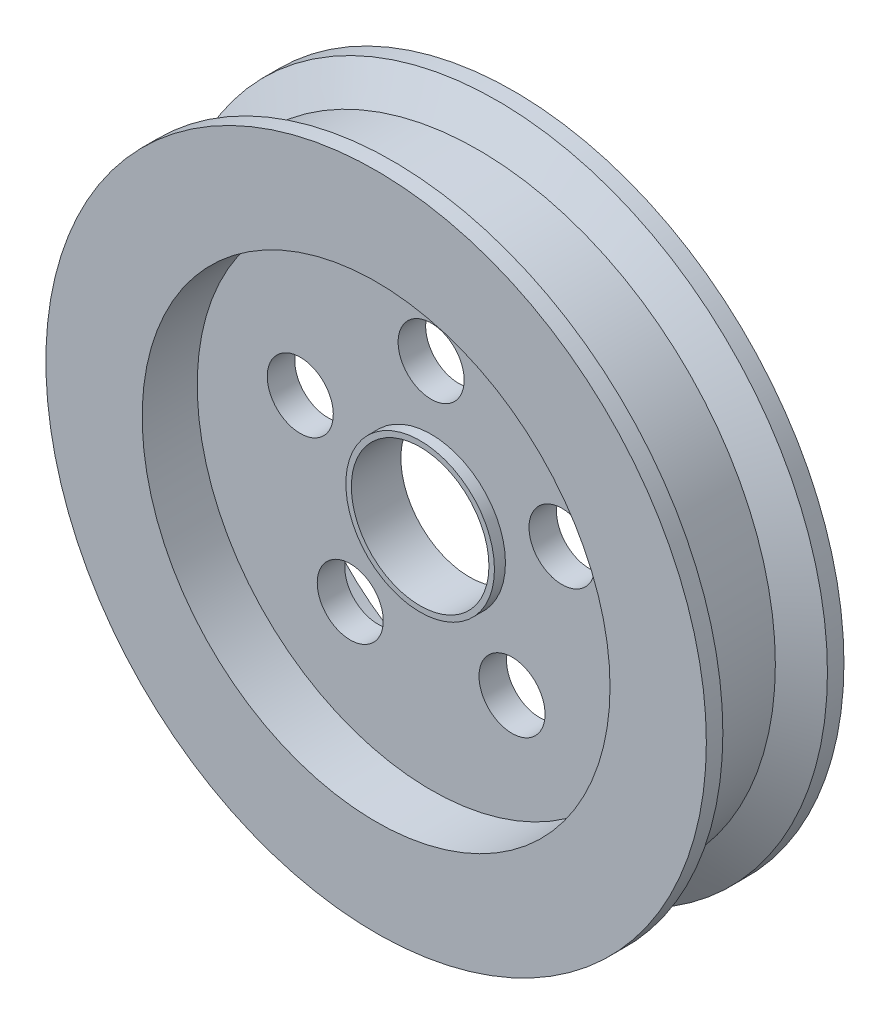
SolidWorks part; units mm, degrees
ref_plane "Front Plane" through (0, 0, 0) normal (0, 0, 1) x (1, 0, 0)
ref_plane "Top Plane" through (0, 0, 0) normal (0, 1, 0) x (1, 0, 0)
ref_plane "Right Plane" through (0, 0, 0) normal (1, 0, 0) x (0, 0, -1)
sketch "Sketch1" plane through (0, 0, 0) normal (0, 0, 1) x (1, 0, 0)
  circle A0 centre (0, 0) radius 60
  circle A1 centre (0, 0) radius 12.5
  dimension "D1" = 120
  dimension "D2" = 25
extrude "Boss-Extrude1" add sketch "Sketch1" along normal mid plane 25
sketch "Sketch2" plane through (0, 0, 12.5) normal (0, 0, 1) x (1, 0, 0)
  circle A0 centre (0, 0) radius 42.5
  dimension "D1" = 85
extrude "Cut-Extrude1" cut sketch "Sketch2" against normal blind 10
mirror "Mirror1" about plane through (0, 0, 0) normal (0, 0, 1) of "Cut-Extrude1"
sketch "Sketch3" plane through (0, 0, 2.5) normal (0, 0, 1) x (1, 0, 0)
  circle A0 centre (0, 25) radius 6
  dimension "D1" = 12
  dimension "D2" = 25
extrude "Cut-Extrude2" cut sketch "Sketch3" against normal through all
pattern_circular "CirPattern1" count 5 over 360 about axis through (0, 0, 0) along (0, 0, 1) of "Cut-Extrude2"
sketch "Sketch4" plane through (0, 0, 0) normal (0, 1, 0) x (1, 0, 0)
  line L0 (0, 0) -> (0, 42.4547) construction
  line L1 (60, 9.5) -> (54, 6.0359)
  line L2 (60, -12.5) -> (60, 12.5) construction
  line L6 (60, -9.5) -> (54, -6.0359)
  line L7 (54, -6.0359) -> (54, 6.0359)
  line L8 (60, -9.5) -> (60, 9.5)
  point P9 (60, 0)
  dimension "D1" = 3
  dimension "D2" = 3
  dimension "D3" = 6
  dimension "D4" = 60
  dimension "D5" = 60
revolve "Cut-Revolve1" cut sketch "Sketch4" angle 360 about L0
sketch "Sketch5" plane through (0, 0, 2.5) normal (0, 0, 1) x (1, 0, 0)
  circle A0 centre (0, 0) radius 13.5
  circle A1 centre (0, 0) radius 12.5 construction
  circle A2 centre (0, 0) radius 12.5
  dimension "D1" = 27
extrude "Boss-Extrude3" add sketch "Sketch5" along normal blind 2 and the other way blind 7
